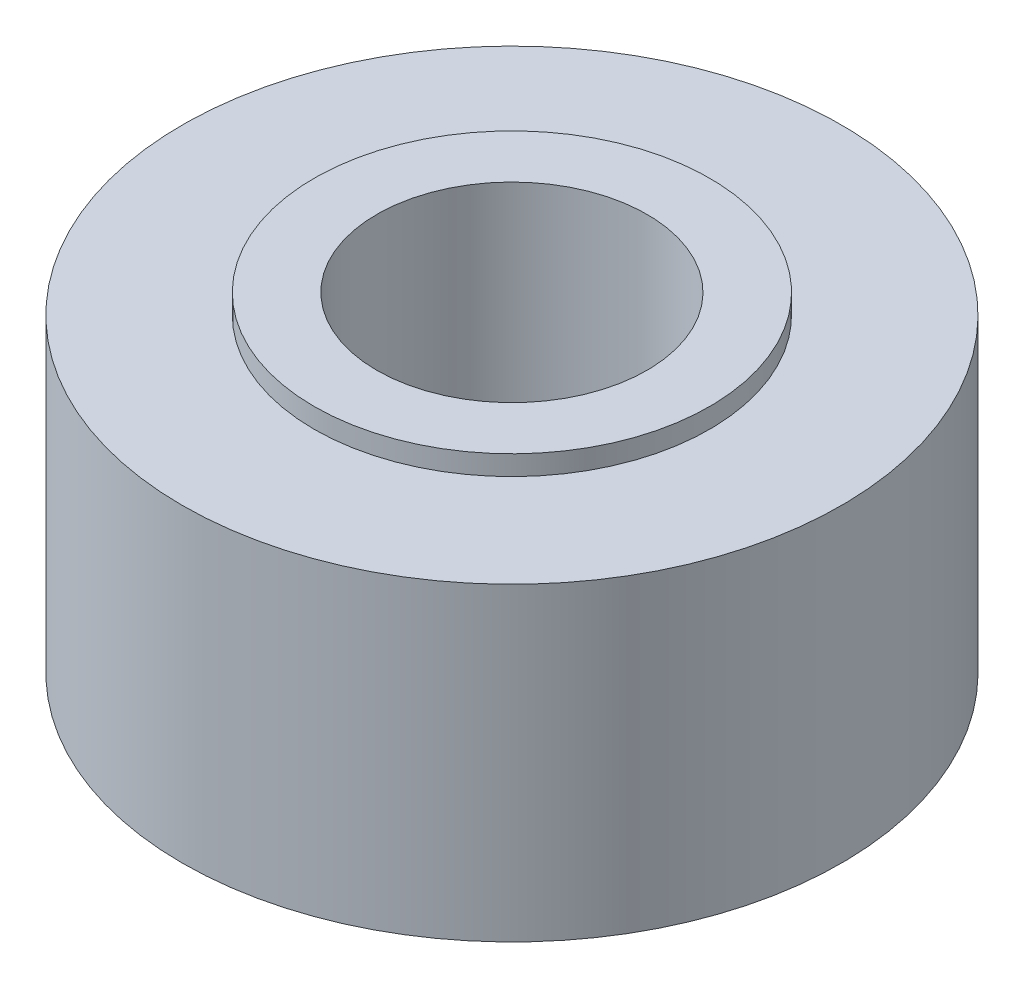
SolidWorks part; units mm, degrees
ref_plane "Front Plane" through (0, 0, 0) normal (0, 0, 1) x (1, 0, 0)
ref_plane "Top Plane" through (0, 0, 0) normal (0, 1, 0) x (1, 0, 0)
ref_plane "Right Plane" through (0, 0, 0) normal (1, 0, 0) x (0, 0, -1)
sketch "스케치1" plane through (0, 0, 0) normal (0, 1, 0) x (1, 0, 0)
  circle A0 centre (0, 0) radius 5
extrude "보스-돌출1" add sketch "스케치1" along normal blind 4.7
sketch "스케치2" plane through (0, 4.7, 0) normal (0, 1, 0) x (1, 0, 0)
  circle A0 centre (0, 0) radius 3
extrude "보스-돌출2" add sketch "스케치2" along normal blind 0.3
sketch "스케치3" plane through (0, 5, 0) normal (0, 1, 0) x (1, 0, 0)
  circle A0 centre (0, 0) radius 2.05
extrude "컷-돌출1" cut sketch "스케치3" against normal through all
